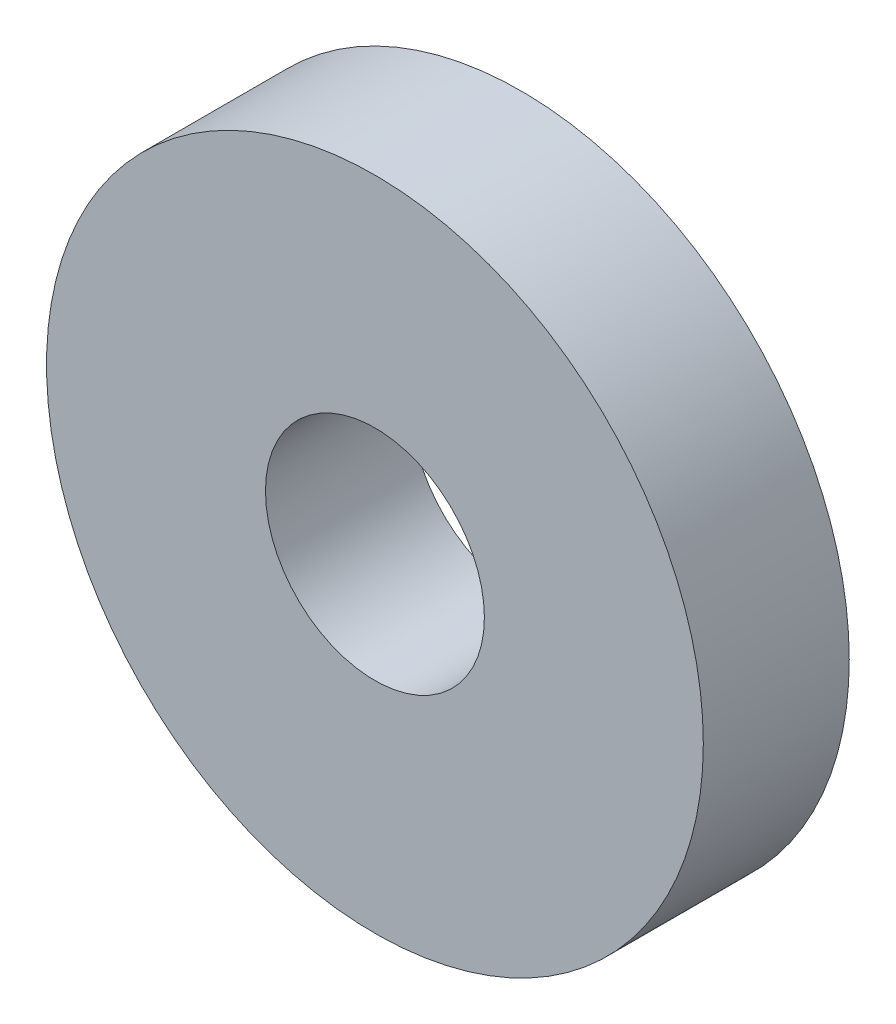
SolidWorks part; units mm, degrees
ref_plane "前视基准面" through (0, 0, 0) normal (0, 0, 1) x (1, 0, 0)
ref_plane "上视基准面" through (0, 0, 0) normal (0, 1, 0) x (1, 0, 0)
ref_plane "右视基准面" through (0, 0, 0) normal (1, 0, 0) x (0, 0, -1)
other "Configuration Table"
sketch "Sketch1" plane through (0, 0, 0) normal (0, 0, 1) x (1, 0, 0)
  circle A0 centre (0, 0) radius 4.5
  circle A1 centre (0, 0) radius 1.5
  dimension "D1" = 9
  dimension "D2" = 3
extrude "Boss-Extrude1" add sketch "Sketch1" along normal blind 2
